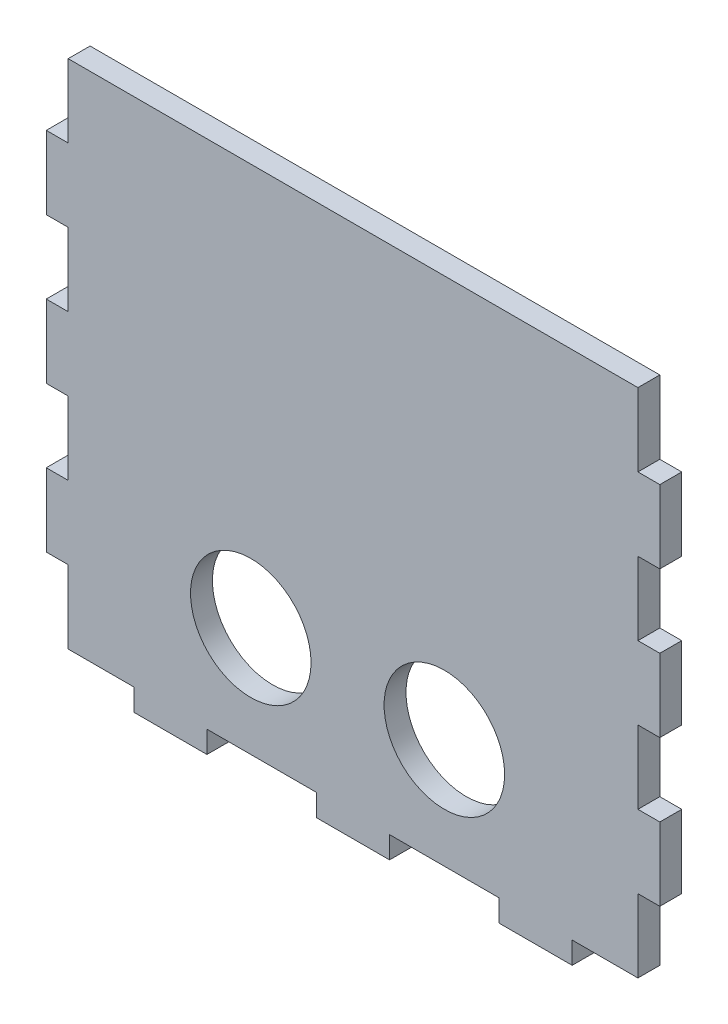
SolidWorks part; units mm, degrees
ref_plane "Plan de face" through (0, 0, 0) normal (0, 0, 1) x (1, 0, 0)
ref_plane "Plan de dessus" through (0, 0, 0) normal (0, 1, 0) x (1, 0, 0)
ref_plane "Plan de droite" through (0, 0, 0) normal (1, 0, 0) x (0, 0, -1)
sketch "Esquisse1" plane through (0, 0, 0) normal (0, 0, 1) x (1, 0, 0)
  line L0 (-69.5385, 40.5978) -> (8.4615, 40.5978)
  line L1 (8.4615, 40.5978) -> (8.4615, 30.5978)
  line L2 (8.4615, 30.5978) -> (11.4615, 30.5978)
  line L3 (11.4615, 30.5978) -> (11.4615, 20.5978)
  line L4 (11.4615, 20.5978) -> (8.4615, 20.5978)
  line L5 (8.4615, 20.5978) -> (8.4615, 10.5978)
  line L6 (8.4615, 10.5978) -> (11.4615, 10.5978)
  line L7 (11.4615, 10.5978) -> (11.4615, 0.5978)
  line L8 (11.4615, 0.5978) -> (8.4615, 0.5978)
  line L9 (8.4615, 0.5978) -> (8.4615, -9.4022)
  line L10 (8.4615, -9.4022) -> (11.4615, -9.4022)
  line L11 (11.4615, -9.4022) -> (11.4615, -19.4022)
  line L12 (11.4615, -19.4022) -> (8.4615, -19.4022)
  line L13 (8.4615, -19.4022) -> (8.4615, -29.4022)
  line L14 (8.4615, -29.4022) -> (-0.5385, -29.4022)
  line L15 (-0.5385, -29.4022) -> (-0.5385, -32.4022)
  line L16 (-0.5385, -32.4022) -> (-10.5385, -32.4022)
  line L17 (-10.5385, -32.4022) -> (-10.5385, -29.4022)
  line L18 (-10.5385, -29.4022) -> (-25.5385, -29.4022)
  line L19 (-25.5385, -29.4022) -> (-25.5385, -32.4022)
  line L23 (-30.5385, -29.4022) -> (-30.5385, 63.9042) construction
  line L26 (-35.5385, -29.4022) -> (-35.5385, -32.4022)
  line L27 (-50.5385, -29.4022) -> (-35.5385, -29.4022)
  line L28 (-50.5385, -32.4022) -> (-50.5385, -29.4022)
  line L29 (-60.5385, -32.4022) -> (-50.5385, -32.4022)
  line L30 (-60.5385, -29.4022) -> (-60.5385, -32.4022)
  line L31 (-69.5385, -29.4022) -> (-60.5385, -29.4022)
  line L32 (-69.5385, -19.4022) -> (-69.5385, -29.4022)
  line L33 (-72.5385, -19.4022) -> (-69.5385, -19.4022)
  line L34 (-72.5385, -9.4022) -> (-72.5385, -19.4022)
  line L35 (-69.5385, -9.4022) -> (-72.5385, -9.4022)
  line L36 (-69.5385, 0.5978) -> (-69.5385, -9.4022)
  line L37 (-72.5385, 0.5978) -> (-69.5385, 0.5978)
  line L38 (-72.5385, 10.5978) -> (-72.5385, 0.5978)
  line L39 (-69.5385, 10.5978) -> (-72.5385, 10.5978)
  line L40 (-69.5385, 20.5978) -> (-69.5385, 10.5978)
  line L41 (-72.5385, 20.5978) -> (-69.5385, 20.5978)
  line L42 (-72.5385, 30.5978) -> (-72.5385, 20.5978)
  line L43 (-69.5385, 30.5978) -> (-72.5385, 30.5978)
  line L44 (-69.5385, 40.5978) -> (-69.5385, 30.5978)
  line L45 (-25.5385, -32.4022) -> (-35.5385, -32.4022)
  circle A0 centre (-18.0385, -14.4022) radius 8.25
  circle A1 centre (-44.5385, -14.4022) radius 8.25
  point P28 (-30.5385, 40.5978)
  dimension "D15" = 16.5
  dimension "D16" = 16.5
  dimension "D1" = 39
  dimension "D2" = 10
  dimension "D3" = 10
  dimension "D4" = 10
  dimension "D5" = 10
  dimension "D6" = 10
  dimension "D7" = 10
  dimension "D8" = 10
  dimension "D9" = 9
  dimension "D10" = 10
  dimension "D11" = 15
  dimension "D13" = 3
  dimension "D14" = 3
  dimension "D17" = 26.5
  dimension "D18" = 25
  dimension "D19" = 55
extrude "Boss.-Extru.1" add sketch "Esquisse1" along normal blind 3
